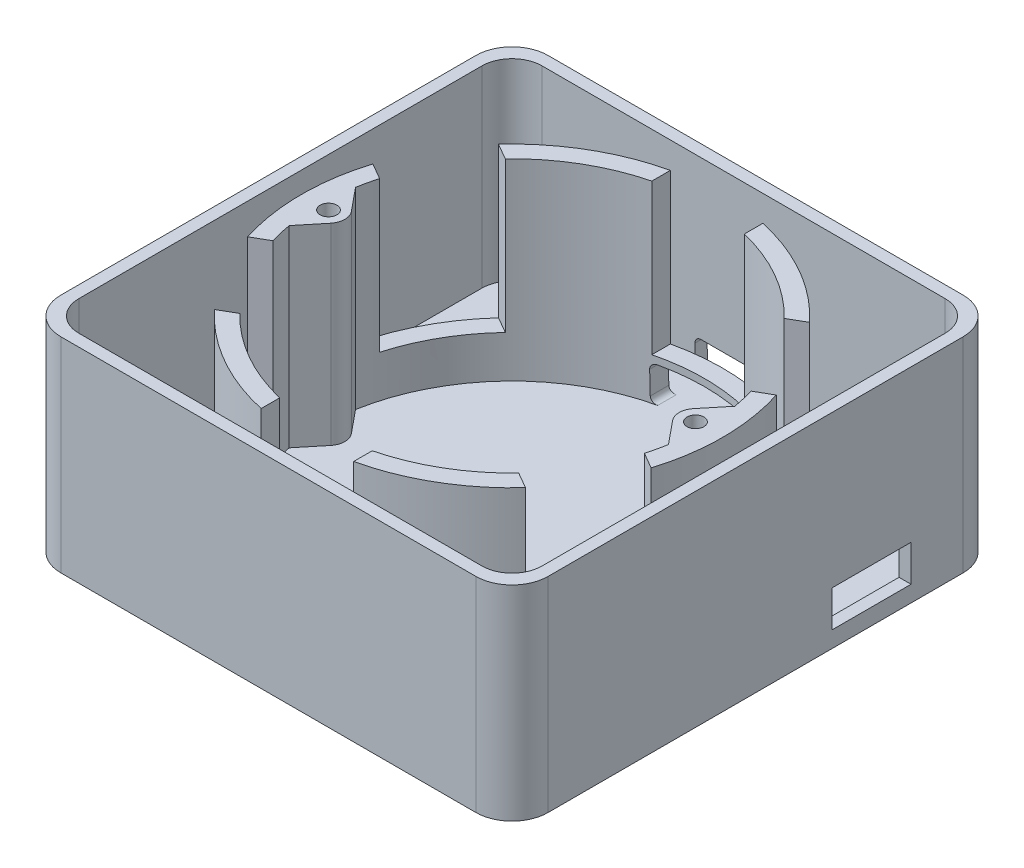
SolidWorks part; units mm, degrees
ref_plane "Спереди" through (0, 0, 0) normal (0, 0, 1) x (1, 0, 0)
ref_plane "Сверху" through (0, 0, 0) normal (0, 1, 0) x (1, 0, 0)
ref_plane "Справа" through (0, 0, 0) normal (1, 0, 0) x (0, 0, -1)
sketch "Sketch1" plane through (0, 0, 0) normal (0, 1, 0) x (1, 0, 0)
  line L0 (68.9109, 42.2105) -> (72.022, 46.0101)
  line L1 (75, 81) -> (73.0182, 81)
  line L2 (81, 75.5) -> (81, 6)
  line L3 (75, 0) -> (6, 0)
  line L7 (40.5, 81) -> (40.5, 79.5)
  line L9 (6, 81) -> (75, 81)
  line L15 (40.5, 81) -> (75, 81)
  line L16 (2, 74) -> (2, 7)
  line L17 (0, 40.5) -> (0, 75)
  line L18 (68.9109, 38.7895) -> (72.022, 34.9899)
  line L19 (0, 40.5) -> (0, 0)
  line L20 (73.0182, 81) -> (75, 81)
  line L21 (81, 75) -> (81, 70.6488)
  line L22 (12.0891, 38.7895) -> (8.978, 34.9899)
  line L23 (12.0891, 42.2105) -> (8.978, 46.0101)
  line L25 (7, 2) -> (74, 2)
  line L30 (7, 79) -> (74, 79)
  line L31 (79.5, 75.5) -> (79, 75.5)
  line L32 (79, 74) -> (79, 7)
  arc A0 (81, 6) -> (75, 0) centre (75, 6) cw
  arc A1 (6, 0) -> (0, 6) centre (6, 6) cw
  arc A2 (0, 75) -> (6, 81) centre (6, 75) cw
  arc A3 (75, 81) -> (81, 75) centre (75, 75) cw
  arc A8 (7, 79) -> (2, 74) centre (7, 74) ccw
  arc A9 (79, 74) -> (74, 79) centre (74, 74) ccw
  arc A10 (72.022, 46.0101) -> (8.978, 46.0101) centre (40.5, 40.5) ccw
  arc A11 (79, 7) -> (74, 2) centre (74, 7) cw
  arc A12 (8.978, 34.9899) -> (72.022, 34.9899) centre (40.5, 40.5) ccw
  arc A13 (72.022, 46.0101) -> (8.978, 46.0101) centre (40.5, 40.5) ccw
  circle A14 centre (40.5, 40.5) radius 35
  arc A15 (8.978, 34.9899) -> (72.022, 34.9899) centre (40.5, 40.5) ccw
  circle A16 centre (10, 40.5) radius 1.4
  arc A17 (68.9109, 42.2105) -> (68.9109, 38.7895) centre (71, 40.5) ccw
  arc A18 (12.0891, 38.7895) -> (12.0891, 42.2105) centre (10, 40.5) ccw
  circle A19 centre (71, 40.5) radius 1.4
  arc A20 (7, 2) -> (2, 7) centre (7, 7) cw
  point P9 (0, 0)
  dimension "D1" = 6
  dimension "D5" = 6
  dimension "D6" = 5
extrude "Boss-Extrude1" add sketch "Sketch1" along normal blind 32
sketch "Sketch2" plane through (0, 0, 0) normal (0, -1, 0) x (1, 0, 0)
  line L1 (6, 0) -> (75, 0)
  line L2 (0, -6) -> (0, -75)
  line L3 (6, -81) -> (75, -81)
  line L4 (81, -6) -> (81, -75)
  arc A0 (75, -81) -> (81, -75) centre (75, -75) ccw
  arc A1 (6, -81) -> (0, -75) centre (6, -75) cw
  arc A2 (0, -6) -> (6, 0) centre (6, -6) cw
  arc A3 (75, 0) -> (81, -6) centre (75, -6) cw
  point P9 (0, 0)
  dimension "D1" = 6
extrude "Boss-Extrude2" add sketch "Sketch2" along normal blind 2 contours L1 A3 L4 A0 L3 A1 L2 A2
sketch "Sketch4" plane through (0, 0, -81) normal (0, 0, -1) x (-1, 0, 0)
  line L4 (-33.5, 0) -> (-47.5, 0)
  line L5 (-48.5, 1) -> (-48.5, 4.8196)
  line L6 (-47.5, 5.8196) -> (-33.4207, 5.8196)
  line L7 (-32.5002, 0.9792) -> (-32.4209, 4.7988)
  arc A0 (-47.5, 0) -> (-48.5, 1) centre (-47.5, 1) cw
  arc A1 (-32.4209, 4.7988) -> (-33.4207, 5.8196) centre (-33.4207, 4.8196) ccw
  arc A2 (-32.5002, 0.9792) -> (-33.5, 0) centre (-33.5, 1) cw
  arc A3 (-48.5, 4.8196) -> (-47.5, 5.8196) centre (-47.5, 4.8196) cw
  point P14 (-40.4603, 5.8196)
  dimension "D1" = 1
sketch "Sketch5" plane through (0, 0, -81) normal (0, 0, -1) x (-1, 0, 0)
extrude "Cut-Extrude2" cut sketch "Sketch4" against normal blind 21
sketch "Sketch6" plane through (0, 32, 0) normal (0, 1, 0) x (1, 0, 0)
  line L0 (67.5807, 65.1329) -> (75.2356, 51.8742)
  line L1 (32.7077, 76.269) -> (48.0175, 76.269)
  line L2 (32.7077, 76.269) -> (32.7077, 70.4248)
  line L3 (32.7077, 70.4248) -> (48.0175, 70.4248)
  line L4 (48.0175, 76.269) -> (48.0175, 70.4248)
  line L5 (67.5807, 65.1329) -> (62.5194, 62.2108)
  line L6 (62.5194, 62.2108) -> (70.1744, 48.952)
  line L7 (75.2356, 51.8742) -> (70.1744, 48.952)
  line L8 (75.3731, 29.3639) -> (67.7181, 16.1051)
  line L9 (75.3731, 29.3639) -> (70.3118, 32.286)
  line L10 (70.3118, 32.286) -> (62.6569, 19.0273)
  line L11 (67.7181, 16.1051) -> (62.6569, 19.0273)
  line L12 (48.2923, 4.731) -> (32.9825, 4.731)
  line L13 (48.2923, 4.731) -> (48.2923, 10.5752)
  line L14 (48.2923, 10.5752) -> (32.9825, 10.5752)
  line L15 (32.9825, 4.731) -> (32.9825, 10.5752)
  line L16 (13.4193, 15.8671) -> (5.7644, 29.1258)
  line L17 (13.4193, 15.8671) -> (18.4806, 18.7892)
  line L18 (18.4806, 18.7892) -> (10.8256, 32.048)
  line L19 (5.7644, 29.1258) -> (10.8256, 32.048)
  line L20 (5.6269, 51.6361) -> (13.2819, 64.8949)
  line L21 (5.6269, 51.6361) -> (10.6882, 48.714)
  line L22 (10.6882, 48.714) -> (18.3431, 61.9727)
  line L23 (13.2819, 64.8949) -> (18.3431, 61.9727)
  point P26 (40.5, 40.5)
  dimension "D1" = 6
extrude "Cut-Extrude3" cut sketch "Sketch6" against normal blind 25
sketch "Sketch7" plane through (0, -2, 0) normal (0, -1, 0) x (-1, 0, 0)
  line L0 (-7.68, 71.616) -> (-7.68, 67.3499)
  line L1 (-11.68, 71.616) -> (-11.68, 67.3499)
  line L2 (-1040.5, 40.5) -> (48959.5, 40.5) construction
  line L3 (-40.5, -959.5) -> (-40.5, 49040.5) construction
  line L4 (-73.32, 71.616) -> (-73.32, 67.3499)
  line L5 (-69.32, 71.616) -> (-69.32, 67.3499)
  line L6 (-69.32, 9.384) -> (-69.32, 13.6501)
  line L7 (-73.32, 9.384) -> (-73.32, 13.6501)
  line L8 (-11.68, 9.384) -> (-11.68, 13.6501)
  line L9 (-7.68, 9.384) -> (-7.68, 13.6501)
  arc A0 (-69.32, 67.3499) -> (-73.32, 67.3499) centre (-71.32, 67.3499) cw
  arc A1 (-7.68, 71.616) -> (-11.68, 71.616) centre (-9.68, 71.616) ccw
  arc A2 (-73.32, 71.616) -> (-69.32, 71.616) centre (-71.32, 71.616) cw
  arc A3 (-73.32, 9.384) -> (-69.32, 9.384) centre (-71.32, 9.384) ccw
  arc A4 (-11.68, 67.3499) -> (-7.68, 67.3499) centre (-9.68, 67.3499) ccw
  arc A5 (-69.32, 13.6501) -> (-73.32, 13.6501) centre (-71.32, 13.6501) ccw
  arc A6 (-11.68, 13.6501) -> (-7.68, 13.6501) centre (-9.68, 13.6501) cw
  arc A7 (-7.68, 9.384) -> (-11.68, 9.384) centre (-9.68, 9.384) cw
extrude "Cut-Extrude4" cut sketch "Sketch7" against normal blind 10
sketch "Sketch8" plane through (81, 0, 0) normal (1, 0, 0) x (0, 0, -1)
  line L1 (66.3383, 0.6981) -> (53.2309, 0.6981)
  line L2 (66.3383, 0.6981) -> (66.3383, 6.7408)
  line L3 (66.3383, 6.7408) -> (53.2309, 6.7408)
  line L4 (53.2309, 0.6981) -> (53.2309, 6.7408)
  point P4 (53.2309, 0.6981)
extrude "Cut-Extrude5" cut sketch "Sketch8" against normal blind 4
